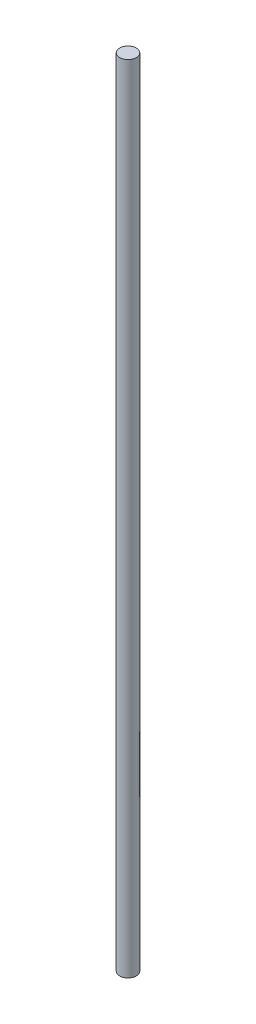
SolidWorks part; units mm, degrees
ref_plane "Front Plane" through (0, 0, 0) normal (0, 0, 1) x (1, 0, 0)
ref_plane "Top Plane" through (0, 0, 0) normal (0, 1, 0) x (1, 0, 0)
ref_plane "Right Plane" through (0, 0, 0) normal (1, 0, 0) x (0, 0, -1)
sketch "Sketch1" plane through (0, 0, 0) normal (0, 1, 0) x (1, 0, 0)
  circle A0 centre (0, 0) radius 4
  dimension "D1" = 8
extrude "Boss-Extrude1" add sketch "Sketch1" along normal blind 382
